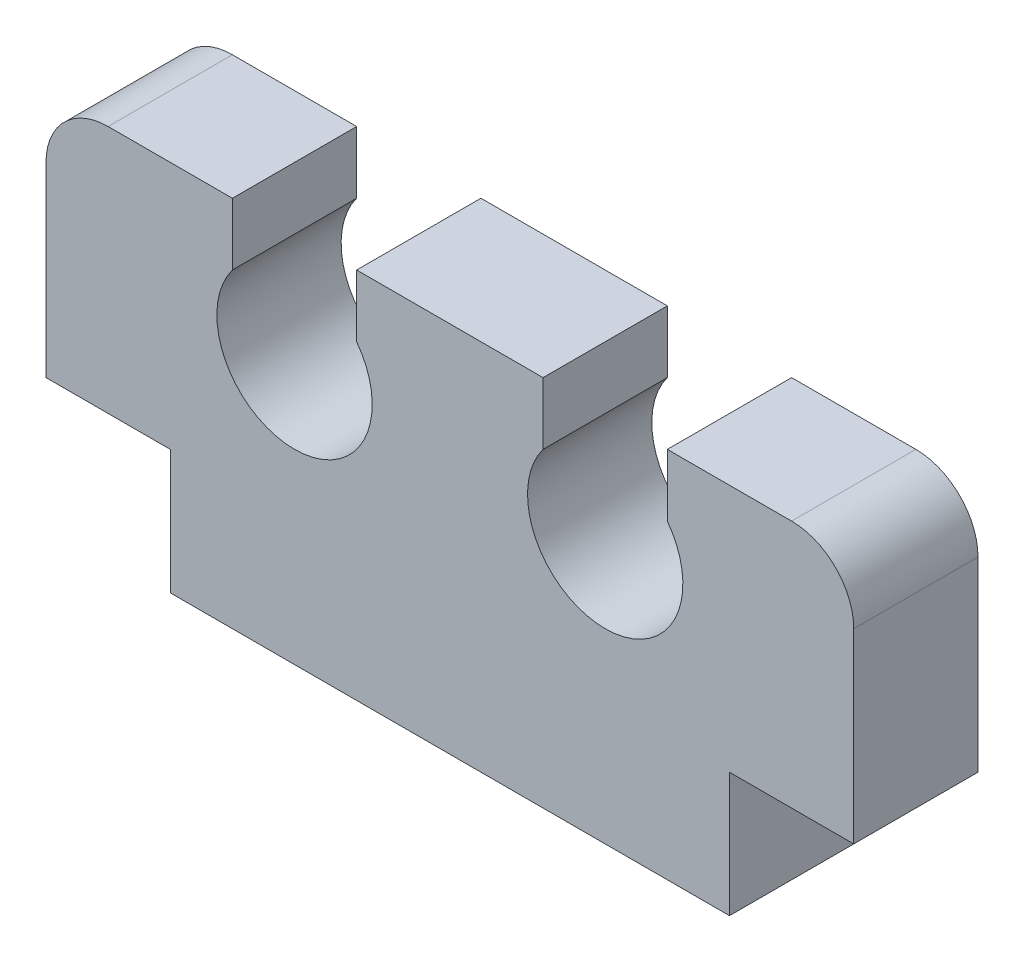
SolidWorks part; units mm, degrees
material "Acrylic (Medium-high impact)"
ref_plane "Front Plane" through (0, 0, 0) normal (0, 0, 1) x (1, 0, 0)
ref_plane "Top Plane" through (0, 0, 0) normal (0, 1, 0) x (1, 0, 0)
ref_plane "Right Plane" through (0, 0, 0) normal (1, 0, 0) x (0, 0, -1)
sketch "Model" plane through (0, 0, 0) normal (0, 0, 1) x (1, 0, 0)
  line L0 (11, 2) -> (11, 5)
  line L1 (-2, 2) -> (-2, 5)
  line L2 (1, 6) -> (-1, 6)
  line L3 (8, 6) -> (10, 6)
  line L4 (0, 0) -> (9, 0)
  line L5 (3, 6) -> (6, 6)
  line L6 (0, 2) -> (0, 0)
  line L7 (9, 2) -> (9, 0)
  line L8 (9, 2) -> (11, 2)
  line L9 (0, 2) -> (-2, 2)
  line L10 (1, 6) -> (1, 5)
  line L11 (3, 6) -> (3, 5)
  line L12 (6, 6) -> (6, 5)
  line L13 (8, 6) -> (8, 5)
  arc A0 (11, 5) -> (10, 6) centre (10, 5) ccw
  arc A1 (-1, 6) -> (-2, 5) centre (-1, 5) ccw
  arc A2 (1, 5) -> (3, 5) centre (2, 4.25) ccw
  arc A3 (6, 5) -> (8, 5) centre (7, 4.25) ccw
  dimension "D1" = 1
  dimension "D2" = 1.25
  dimension "D3" = 2
  dimension "D4" = 6
extrude "Boss-Extrude1" add sketch "Model" along normal blind 2
